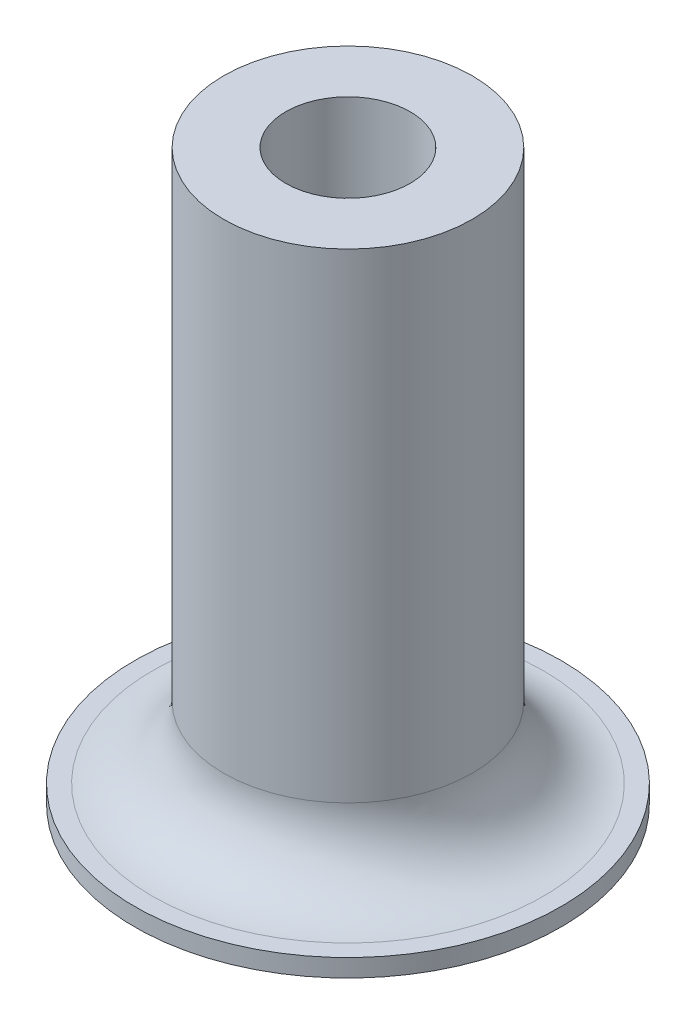
SolidWorks part; units mm, degrees
ref_plane "Alzado" through (0, 0, 0) normal (0, 0, 1) x (1, 0, 0)
ref_plane "Planta" through (0, 0, 0) normal (0, 1, 0) x (1, 0, 0)
ref_plane "Vista lateral" through (0, 0, 0) normal (1, 0, 0) x (0, 0, -1)
sketch "Croquis1" plane through (0, 0, 0) normal (0, 1, 0) x (1, 0, 0)
  circle A0 centre (0, 0) radius 3.5
  circle A1 centre (0, 0) radius 7
  dimension "D1" = 14
  dimension "D2" = 7
extrude "Saliente-Extruir1" add sketch "Croquis1" along normal blind 32 contours A1 A0
sketch "Croquis2" plane through (0, 0, 0) normal (0, -1, 0) x (1, 0, 0)
  circle A0 centre (0, 0) radius 7 construction
  circle A1 centre (0, 0) radius 7
  circle A2 centre (0, 0) radius 12
  dimension "D1" = 5
extrude "Saliente-Extruir2" add sketch "Croquis2" against normal blind 1
fillet "Redondeo1" radius 4 1 edges at (0, 1, -7)
